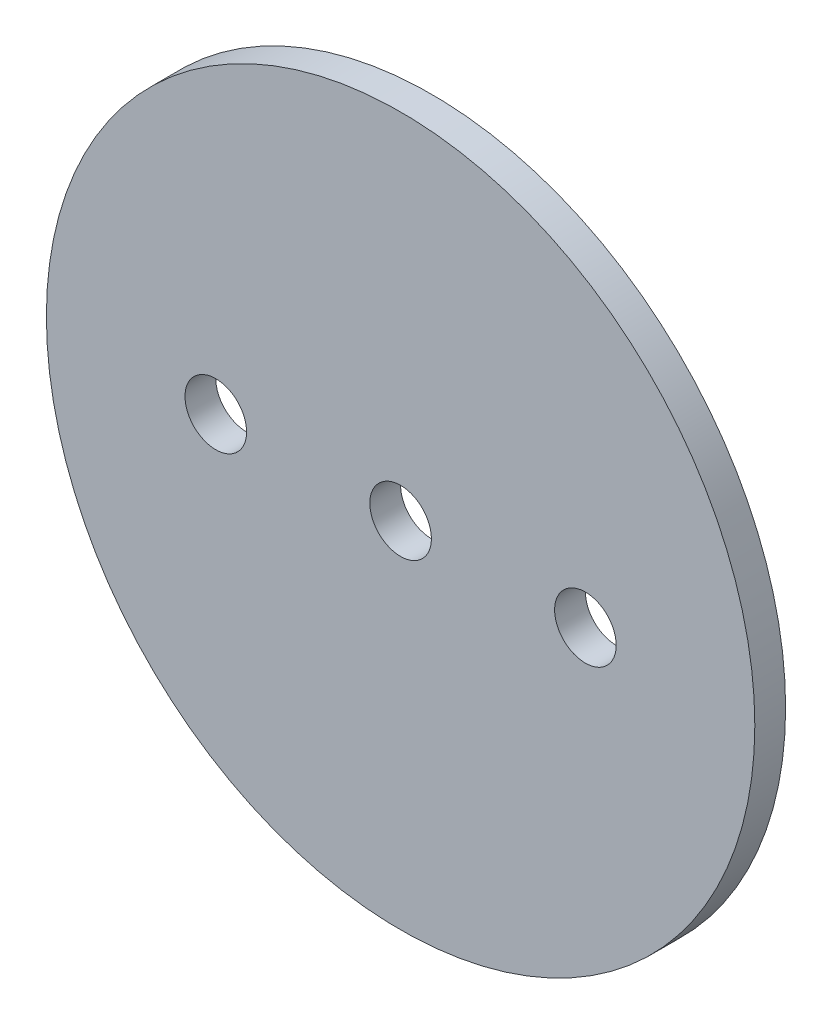
SolidWorks part; units mm, degrees
ref_plane "Front Plane" through (0, 0, 0) normal (0, 0, 1) x (1, 0, 0)
ref_plane "Top Plane" through (0, 0, 0) normal (0, 1, 0) x (1, 0, 0)
ref_plane "Right Plane" through (0, 0, 0) normal (1, 0, 0) x (0, 0, -1)
sketch "Sketch1" plane through (0, 0, 0) normal (0, 0, 1) x (1, 0, 0)
  circle A0 centre (0, 0) radius 36.5125
  dimension "D1" = 73.025
extrude "Boss-Extrude1" add sketch "Sketch1" along normal mid plane 3.175
sketch "Sketch2" plane through (0, 0, 1.5875) normal (0, 0, 1) x (1, 0, 0)
  line L0 (-1000, 0) -> (49000, 0) construction
  point P1 (0, 0)
  point P4 (19.05, 0)
  point P5 (-19.05, 0)
  dimension "D1" = 19.05
  dimension "D2" = 38.1
hole_wizard "1/4 (0.25) Diameter Hole1" positions "Sketch2" profile "Sketch3" hole size "1/4" standard "ANSI Inch" end condition through all
sketch "Sketch3" plane through (-19.05, 0, 1.5875) normal (1, 0, 0) x (0, -1, 0)
  line L0 (0, 0) -> (0, 3.175)
  line L1 (0, 3.175) -> (3.175, 3.175)
  line L2 (3.175, 3.175) -> (3.175, 0)
  line L5 (3.175, 0) -> (0, 0)
  line L11 (0, -6.35) -> (0, 107.95) construction
  dimension "Thru Hole Dia." = 6.35
  dimension "Thru Hole Depth" = 3.175
equation "\"AIRFRAME_OD\"= 3.142in"
equation "\"AIRFRAME_ID\"= 3.00in"
equation "\"FLAT_T\"= 0.125in"
equation "\"NOSE_EXP_L\"= 3.5in"
equation "\"NOSE_SHOULDER_L\"= 5in"
equation "\"MAIN_L\"= 30in"
equation "\"RECO_COUP_L\"= 6in"
equation "\"RECO_SWITCH_L\"= 1.5in"
equation "\"DROGUE_L\"= 14in"
equation "\"ATS_FORE_COUP_L\"= 4in"
equation "\"ATS_AFT_COUP_L\"= 2.5in"
equation "\"LOWER_L\"= 16in"
equation "\"FIN_N\"= 4"
equation "\"CR_AFT_X\"= 0.5in"
equation "\"CR_FORE_X\"= 6in"
equation "\"FIN_ROOT\"= 5in"
equation "\"FIN_X\"= 0.75in"
equation "\"MOTOR_OD\"= 2.25in"
equation "\"MOTOR_ID\"= 2.126in"
equation "\"COUPLER_OD\"= 2.998in"
equation "\"COUPLER_ID\"= 2.875in"
equation "\"D1@Sketch1\"=\"COUPLER_ID\""
equation "\"D1@Boss-Extrude1\"=\"FLAT_T\""
equation "\"RECO_ROD_X\"= 1.5in"
equation "\"ATS_ROD_X\"= 2in"
equation "\"D1@Sketch2\"=\"RECO_ROD_X\"*0.5"
equation "\"D2@Sketch2\"=\"RECO_ROD_X\""
